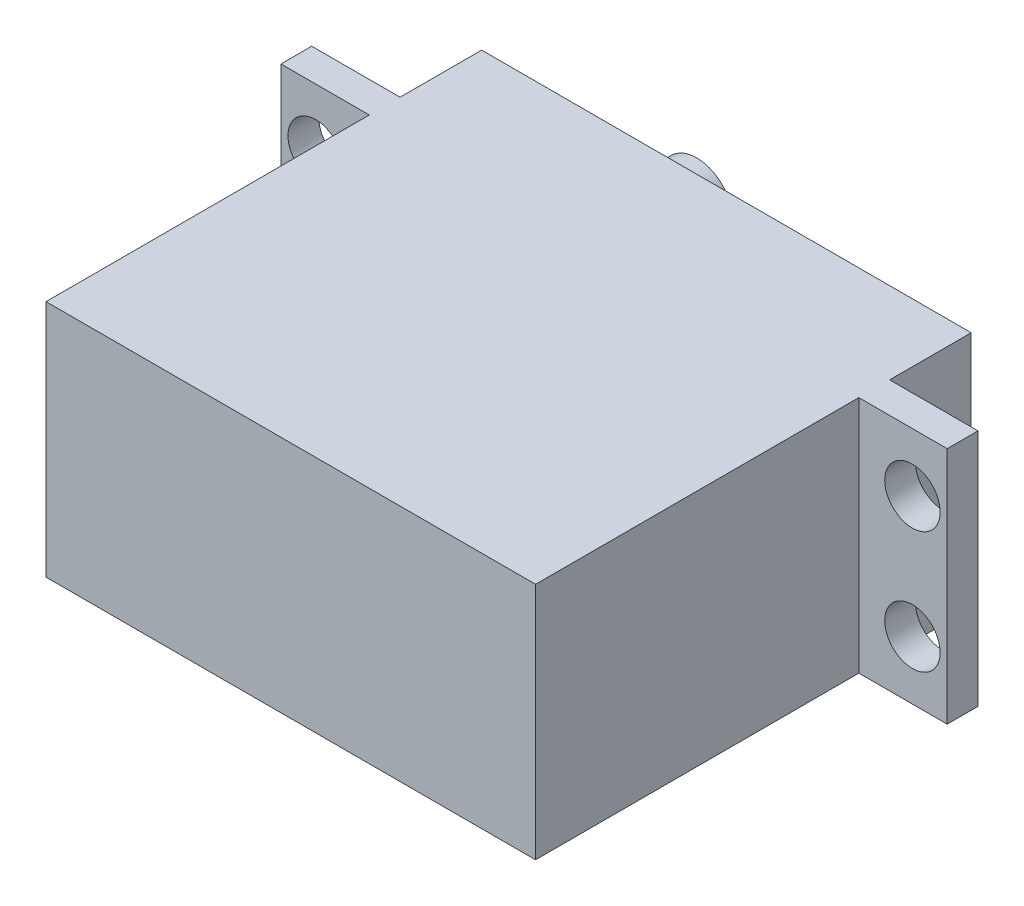
SolidWorks part; units mm, degrees
material "ABS PC"
ref_plane "Front Plane" through (0, 0, 0) normal (0, 0, 1) x (1, 0, 0)
ref_plane "Top Plane" through (0, 0, 0) normal (0, 1, 0) x (1, 0, 0)
ref_plane "Right Plane" through (0, 0, 0) normal (1, 0, 0) x (0, 0, -1)
sketch "Sketch1" plane through (0, 0, 0) normal (0, 1, 0) x (1, 0, 0)
  line L0 (0, 29.21) -> (0, 35.941)
  line L1 (0, 0) -> (40.386, 0)
  line L2 (0, 0) -> (0, 26.67)
  line L3 (0, 35.941) -> (40.386, 35.941)
  line L4 (40.386, 0) -> (40.386, 26.67)
  line L5 (0, 29.21) -> (-7.2898, 29.21)
  line L6 (40.386, 29.21) -> (40.386, 35.941)
  line L7 (0, 26.67) -> (-7.2898, 26.67)
  line L8 (-7.2898, 29.21) -> (-7.2898, 26.67)
  line L9 (40.386, 26.67) -> (47.6758, 26.67)
  line L11 (40.386, 29.21) -> (47.6758, 29.21)
  line L12 (47.6758, 26.67) -> (47.6758, 29.21)
  dimension "D1" = 35.941
  dimension "D2" = 40.386
  dimension "D3" = 7.2898
  dimension "D4" = 7.2898
  dimension "D5" = 2.54
  dimension "D6" = 2.54
  dimension "D7" = 26.67
  dimension "D8" = 26.67
extrude "Boss-Extrude1" add sketch "Sketch1" along normal blind 19.685
sketch "Sketch3" plane through (0, 0, -35.941) normal (0, 0, -1) x (-1, 0, 0)
  line L0 (-40.386, 0) -> (0, 0) construction
  line L1 (0, 19.685) -> (0, 0) construction
  circle A0 centre (-9.7155, 9.8425) radius 2.9845
  point P4 (-12.7, 9.8425)
  dimension "D1" = 5.969
  dimension "D2" = 9.8425
  dimension "D3" = 12.7
extrude "Boss-Extrude2" add sketch "Sketch3" along normal blind 8.0264
sketch "Sketch4" plane through (0, 0, -29.21) normal (0, 0, -1) x (-1, 0, 0)
  line L0 (-47.6758, 19.685) -> (-40.386, 19.685) construction
  line L1 (-47.6758, 19.685) -> (-47.6758, 0) construction
  line L2 (-47.6758, 0) -> (-40.386, 0) construction
  line L3 (7.2898, 19.685) -> (7.2898, 0) construction
  line L4 (0, 19.685) -> (7.2898, 19.685) construction
  line L6 (0, 0) -> (7.2898, 0) construction
  circle A0 centre (-44.8056, 14.859) radius 2.286
  circle A1 centre (-44.8056, 4.826) radius 2.286
  circle A2 centre (4.4196, 14.859) radius 2.286
  circle A3 centre (4.4196, 4.826) radius 2.286
  dimension "D9" = 4.572
  dimension "D10" = 4.572
  dimension "D11" = 4.572
  dimension "D12" = 4.572
  dimension "D1" = 4.826
  dimension "D2" = 2.8702
  dimension "D3" = 4.826
  dimension "D4" = 2.8702
  dimension "D5" = 2.8702
  dimension "D6" = 2.8702
  dimension "D7" = 4.826
  dimension "D8" = 4.826
extrude "Cut-Extrude1" cut sketch "Sketch4" against normal up to next
